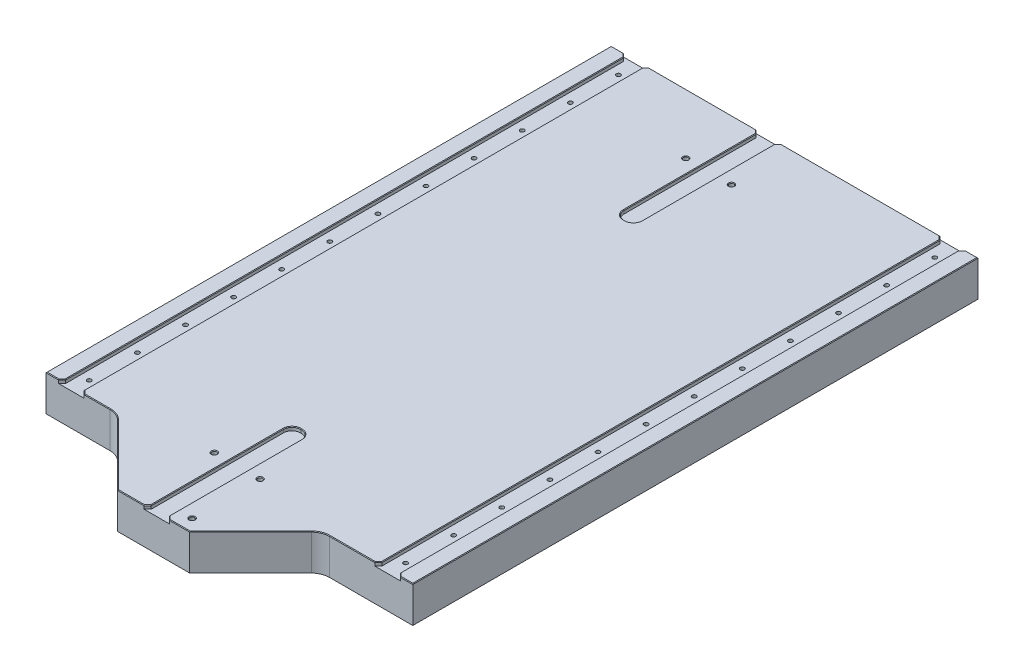
SolidWorks part; units mm, degrees
material "Acrylic (Medium-high impact)"
ref_plane "Front Plane" through (0, 0, 0) normal (0, 0, 1) x (1, 0, 0)
ref_plane "Top Plane" through (0, 0, 0) normal (0, 1, 0) x (1, 0, 0)
ref_plane "Right Plane" through (0, 0, 0) normal (1, 0, 0) x (0, 0, -1)
sketch "Sketch1" plane through (0, 0, 0) normal (0, 1, 0) x (1, 0, 0)
  line L0 (-93, -235) -> (-38, -290)
  line L1 (-152.5, -235) -> (-93, -235)
  line L2 (-152.5, -235) -> (-152.5, 235)
  line L3 (-152.5, 235) -> (152.5, 235)
  line L4 (152.5, -235) -> (152.5, 235)
  line L5 (-152.5, -235) -> (152.5, 235) construction
  line L6 (-152.5, 235) -> (152.5, -235) construction
  line L7 (-38, -290) -> (22, -290)
  line L8 (22, -290) -> (77, -235)
  line L10 (77, -235) -> (152.5, -235)
  point P0 (0, 0)
  dimension "D1" = 305
  dimension "D2" = 470
  dimension "D3" = 45
  dimension "D4" = 45
  dimension "D5" = 55
  dimension "D6" = 22
  dimension "D7" = 60
extrude "Boss-Extrude1" add sketch "Sketch1" along normal blind 30
sketch "Sketch2" plane through (0, 0, 0) normal (0, 1, 0) x (1, 0, 0)
  line L0 (152.5, 235) -> (-152.5, 235) construction
  line L1 (-152.5, 235) -> (-152.5, -235) construction
  line L3 (-152.5, -235) -> (-93, -235) construction
  line L4 (0, 235) -> (0, -235) construction
  line L5 (152.5, 235) -> (-152.5, 235) construction
  line L6 (-152.5, -235) -> (-93, -235) construction
  circle A0 centre (-131.5, 220) radius 1.75
  circle A1 centre (131.5, 220) radius 1.75
  circle A4 centre (13.5, -223) radius 2
  circle A5 centre (-24.5, -223) radius 2
  circle A6 centre (-40.5, 185) radius 2
  circle A7 centre (-2.5, 185) radius 2
  circle A8 centre (131.5, -20) radius 1.75 [skipped]
  circle A9 centre (-131.5, -20) radius 1.75 [skipped]
  circle A10 centre (-131.5, 180) radius 1.75
  circle A11 centre (131.5, 180) radius 1.75
  circle A12 centre (-131.5, 140) radius 1.75
  circle A13 centre (131.5, 140) radius 1.75
  circle A14 centre (-131.5, 100) radius 1.75
  circle A15 centre (131.5, 100) radius 1.75
  circle A16 centre (-131.5, 60) radius 1.75
  circle A17 centre (131.5, 60) radius 1.75
  circle A18 centre (-131.5, 20) radius 1.75
  circle A19 centre (131.5, 20) radius 1.75
  circle A20 centre (-131.5, -20) radius 1.75
  circle A21 centre (131.5, -20) radius 1.75
  circle A22 centre (-131.5, -60) radius 1.75
  circle A23 centre (131.5, -60) radius 1.75
  circle A24 centre (-131.5, -100) radius 1.75
  circle A25 centre (131.5, -100) radius 1.75
  circle A26 centre (-131.5, -140) radius 1.75
  circle A27 centre (131.5, -140) radius 1.75
  circle A28 centre (-131.5, -180) radius 1.75
  circle A29 centre (131.5, -180) radius 1.75
  circle A30 centre (-131.5, -220) radius 1.75
  circle A31 centre (131.5, -220) radius 1.75
  circle A32 centre (13.5, -279.5) radius 2
  dimension "D5" = 3.5
  dimension "D8" = 131.5
  dimension "D9" = 38
  dimension "D10" = 4
  dimension "D11" = 128
  dimension "D12" = 12
  dimension "D13" = 38
  dimension "D14" = 112
  dimension "D15" = 50
  dimension "D3" = 15
  dimension "D4" = 263
  dimension "D6" = 12
  dimension "D7" = 40
  dimension "D16" = 56.5
  dimension "D1" = 2
  dimension "D2" = 2
extrude "Cut-Extrude1" cut sketch "Sketch2" along normal through all
sketch "Sketch3" plane through (0, 30, 0) normal (0, 1, 0) x (1, 0, 0)
  line L0 (152.5, 235) -> (-152.5, 235) construction
  line L1 (-123.875, 235) -> (-139.125, 235)
  line L2 (-123.875, 235) -> (-123.875, -235)
  line L3 (-123.875, -235) -> (-139.125, -235)
  line L4 (-139.125, 235) -> (-139.125, -235)
  line L5 (-152.5, -235) -> (-93, -235) construction
  line L6 (0, 0) -> (0, 235) construction
  line L7 (-131.5, 235) -> (-131.5, 220) construction
  line L8 (123.875, -235) -> (139.125, -235)
  line L9 (123.875, 235) -> (123.875, -235)
  line L10 (123.875, 235) -> (139.125, 235)
  line L11 (131.5, 235) -> (131.5, 220) construction
  line L12 (139.125, 235) -> (139.125, -235)
  dimension "D1" = 15.25
extrude "Cut-Extrude2" cut sketch "Sketch3" against normal blind 3
sketch "Sketch4" plane through (0, 30, 0) normal (0, 1, 0) x (1, 0, 0)
  line L0 (13.5, -223) -> (-24.5, -223) construction
  line L1 (-5.5, -223) -> (-5.5, -230) construction
  line L2 (-38, -290) -> (22, -290) construction
  line L3 (2, -290) -> (-13, -290)
  line L4 (2, -290) -> (2, -170)
  line L5 (2, -170) -> (-13, -170)
  line L6 (-13, -290) -> (-13, -170)
  line L7 (2, -290) -> (-13, -170) construction
  line L8 (2, -170) -> (-13, -290) construction
  line L9 (-2.5, 185) -> (-40.5, 185) construction
  line L10 (-21.5, 185) -> (-21.5, 175) construction
  line L11 (123.875, 235) -> (-123.875, 235) construction
  line L12 (-14, 115) -> (-29, 115)
  line L13 (-14, 115) -> (-14, 235)
  line L14 (-14, 235) -> (-29, 235)
  line L15 (-29, 115) -> (-29, 235)
  line L16 (-14, 115) -> (-29, 235) construction
  line L17 (-14, 235) -> (-29, 115) construction
  dimension "D1" = 120
  dimension "D2" = 15
  dimension "D3" = 120
extrude "Cut-Extrude3" cut sketch "Sketch4" against normal blind 3
fillet "Fillet1" radius 7 4 edges at (-29, 28.5, -115) (-14, 28.5, -115) (-13, 28.5, 170) (2, 28.5, 170)
fillet "Fillet2" radius 15 2 edges at (77, 15, 235) (-93, 15, 235)
chamfer "Chamfer1" distance 3 angle 45 12 edges at (-139.125, 28.5, 235) (-123.875, 28.5, 235) (139.125, 28.5, 235) (123.875, 28.5, 235) (139.125, 28.5, -235) (123.875, 28.5, -235) (-123.875, 28.5, -235) (-139.125, 28.5, -235) (-14, 28.5, -235) (-29, 28.5, -235) (2, 28.5, 290) (-13, 28.5, 290)
chamfer "Chamfer2" distance 0.5 angle 45 47 edges at (140.625, 30, -233.5) (147.3125, 30, -235) (152.5, 30, 0) (147.3125, 30, 235) (140.625, 30, 233.5) (139.125, 30, 0) (-122.375, 30, -233.5) (-76.4375, 30, -235) (-30.5, 30, -233.5) (-29, 30, -177) (-26.9497, 30, -117.0503) (-21.5, 30, -115) (-16.0503, 30, -117.0503) (-14, 30, -177) (-12.5, 30, -233.5) (54.9375, 30, -235) (122.375, 30, -233.5) (123.875, 30, 0) (122.375, 30, 233.5) (102.0441, 30, 235) (77.473, 30, 236.1418) (47.3033, 30, 264.6967) (13.5, 30, 290) (3.5, 30, 288.5) (2, 30, 232) (-0.0503, 30, 172.0503) (-5.5, 30, 170) (-10.9497, 30, 172.0503) (-13, 30, 232) (-14.5, 30, 288.5) (-27, 30, 290) (-63.3033, 30, 264.6967) (-93.473, 30, 236.1418) (-110.0441, 30, 235) (-122.375, 30, 233.5) (-123.875, 30, 0) (13.5, 30, 281.5) (-2.5, 30, -183) (-40.5, 30, -183) (-24.5, 30, 225) (13.5, 30, 225) (-152.5, 30, 0) (-147.3125, 30, -235) (-140.625, 30, -233.5) (-139.125, 30, 0) (-140.625, 30, 233.5) (-147.3125, 30, 235)
